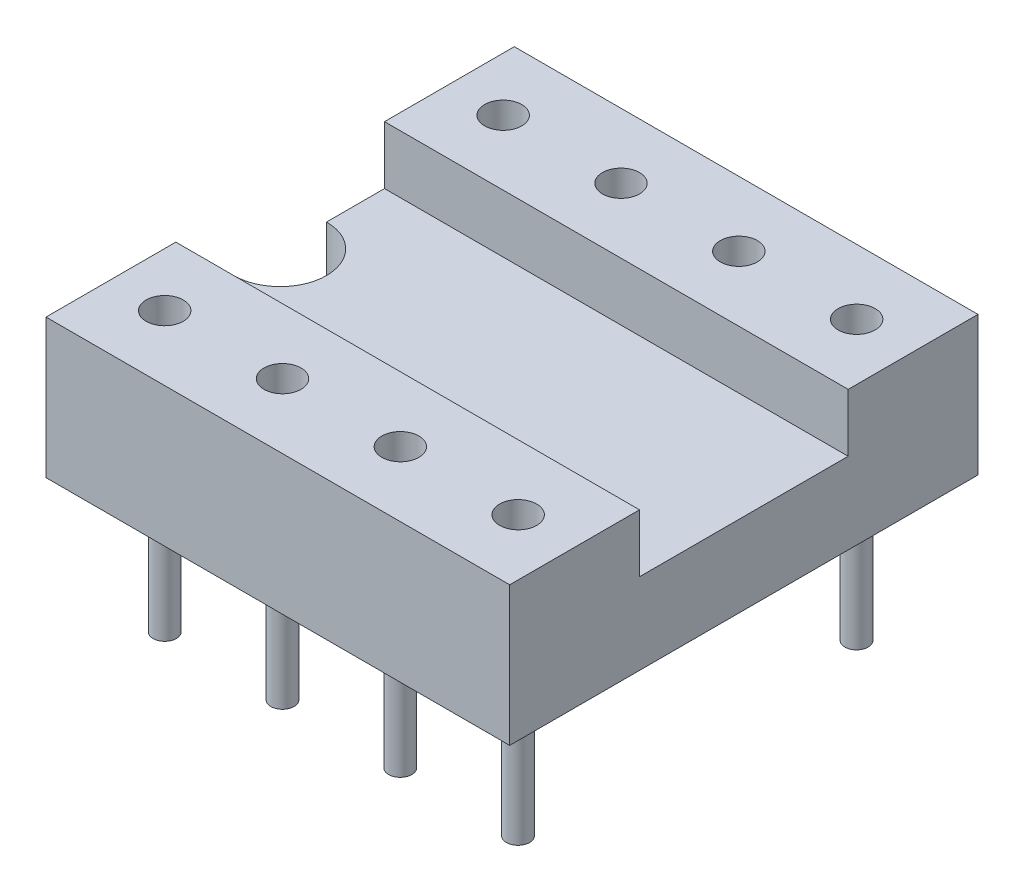
SolidWorks part; units mm, degrees
ref_plane "Plan de face" through (0, 0, 0) normal (0, 0, 1) x (1, 0, 0)
ref_plane "Plan de dessus" through (0, 0, 0) normal (0, 1, 0) x (1, 0, 0)
ref_plane "Plan de droite" through (0, 0, 0) normal (1, 0, 0) x (0, 0, -1)
sketch "Esquisse1" plane through (0, 0, 0) normal (1, 0, 0) x (0, 0, -1)
  line L0 (12.2051, 0) -> (-23.3437, 0) construction
  line L1 (0, -4.6214) -> (0, 25.9507) construction
  line L2 (-5.7968, 1.75) -> (2.763, 1.75) construction
  line L3 (5.7565, 3) -> (-6.8307, 3) construction
  line L4 (5.05, 3.8077) -> (5.05, -1.0493) construction
  line L5 (-5.05, 3.7235) -> (-5.05, -1.0493) construction
  line L6 (-2.25, 3.5071) -> (-2.25, 0.8142) construction
  line L7 (2.25, 3.5071) -> (2.25, 0.8142) construction
  line L8 (-2.25, 1.75) -> (-2.25, 3)
  line L9 (-2.25, 3) -> (-5.05, 3)
  line L10 (-5.05, 3) -> (-5.05, 0)
  line L11 (-5.05, 0) -> (5.05, 0)
  line L12 (5.05, 0) -> (5.05, 3)
  line L13 (5.05, 3) -> (2.25, 3)
  line L14 (2.25, 3) -> (2.25, 1.75)
  line L15 (2.25, 1.75) -> (-2.25, 1.75)
  dimension "D1" = 1.75
  dimension "D2" = 3
  dimension "D3" = 5.05
  dimension "D4" = 5.05
  dimension "D5" = 2.8
  dimension "D6" = 2.8
extrude "Extrusion1" add sketch "Esquisse1" along normal blind 10
sketch "Esquisse2" plane through (0, 1.75, 0) normal (0, 1, 0) x (-1, 0, 0)
  line L0 (0, -1) -> (0, 1)
  arc A0 (0, 1) -> (0, -1) centre (0, 0) ccw
extrude "Enlèv. mat.-Extru.1" cut sketch "Esquisse2" against normal through all
sketch "Esquisse3" plane through (0, 3, 0) normal (0, 1, 0) x (-1, 0, 0)
  line L0 (-13.1576, 5.05) -> (2.3638, 5.05) construction
  line L1 (0, 6.1465) -> (0, -6.3771) construction
  line L2 (1.5124, 0) -> (-12.9979, 0) construction
  line L3 (1.0512, 3.65) -> (-15.6055, 3.65) construction
  line L4 (-1.16, 6.2884) -> (-1.16, 1.7827) construction
  circle A0 centre (-1.16, 3.65) radius 0.4
  circle A1 centre (-1.16, -3.65) radius 0.4
  circle A2 centre (-3.701, 3.65) radius 0.4
  circle A3 centre (-3.701, -3.65) radius 0.4
  circle A4 centre (-6.242, 3.65) radius 0.4
  circle A5 centre (-6.242, -3.65) radius 0.4
  circle A6 centre (-8.783, 3.65) radius 0.4
  circle A7 centre (-8.783, -3.65) radius 0.4
  dimension "D1" = 1.4
  dimension "D2" = 1.16
extrude "Enlèv. mat.-Extru.2" cut sketch "Esquisse3" against normal blind 2.5
sketch "Esquisse5" plane through (0, 0, 0) normal (0, -1, 0) x (1, 0, 0)
  line L0 (-0.4263, 0) -> (10.6481, 0) construction
  circle A0 centre (1.16, 3.65) radius 0.25
  circle A1 centre (1.16, -3.65) radius 0.25
  circle A2 centre (3.7, -3.65) radius 0.25
  circle A3 centre (3.7, 3.65) radius 0.25
  circle A4 centre (6.24, -3.65) radius 0.25
  circle A5 centre (6.24, 3.65) radius 0.25
  circle A6 centre (8.78, -3.65) radius 0.25
  circle A7 centre (8.78, 3.65) radius 0.25
extrude "Extrusion2" add sketch "Esquisse5" along normal blind 3
